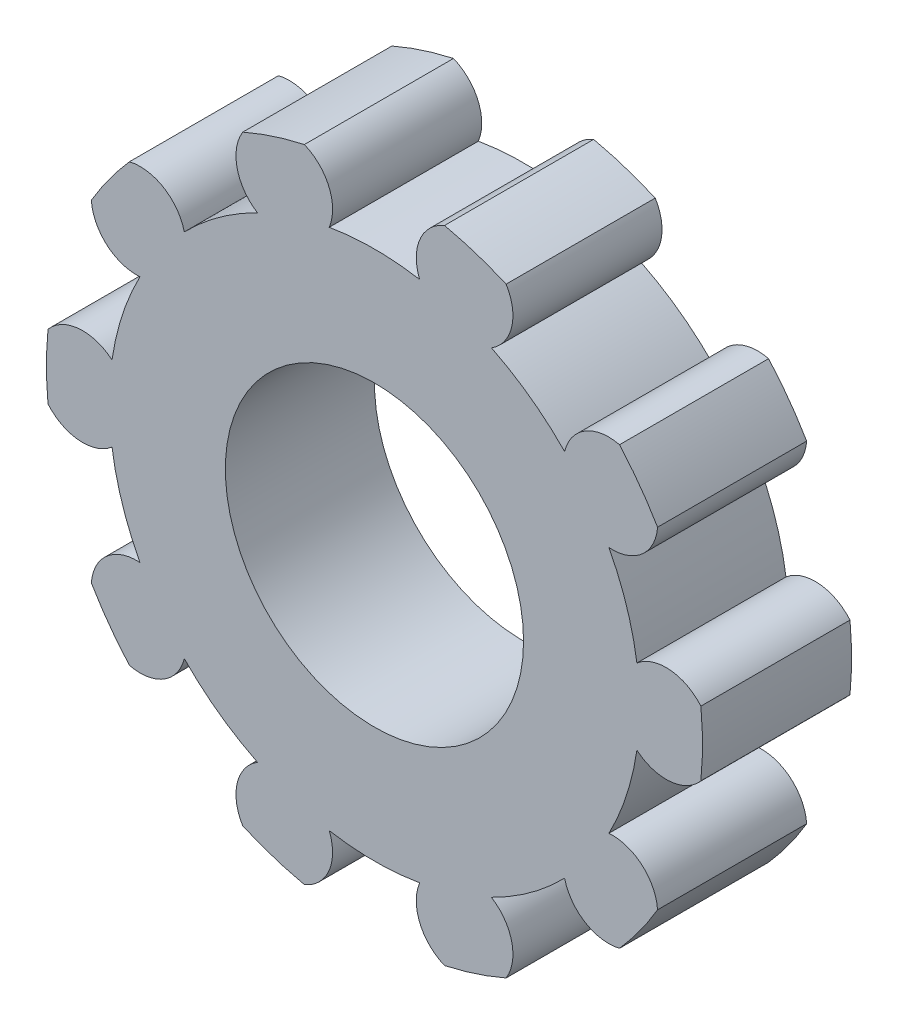
SolidWorks part; units mm, degrees
ref_plane "Front Plane" through (0, 0, 0) normal (0, 0, 1) x (1, 0, 0)
ref_plane "Top Plane" through (0, 0, 0) normal (0, 1, 0) x (1, 0, 0)
ref_plane "Right Plane" through (0, 0, 0) normal (1, 0, 0) x (0, 0, -1)
sketch "Sketch1" plane through (0, 0, 0) normal (0, 0, 1) x (1, 0, 0)
  circle A0 centre (0, 0) radius 6
  circle A1 centre (0, 0) radius 13.2
extrude "Boss-Extrude1" add sketch "Sketch1" along normal blind 6
sketch "Sketch2" plane through (0, 0, 6) normal (0, 0, 1) x (1, 0, 0)
  line L0 (0, 0) -> (0, 15.2) construction
  line L1 (-1.8199, 15.2) -> (0, 0) construction
  line L2 (1.8199, 15.2) -> (0, 0) construction
  arc A0 (-1.8199, 12) -> (1.8199, 12) centre (0, 0) cw
  arc A1 (-2.8199, 12.8953) -> (2.8199, 12.8953) centre (0, 0) cw
  arc A2 (-1.8199, 10.512) -> (1.8199, 10.512) centre (0, 0) cw
  arc A3 (-2.8199, 12.8953) -> (-1.8199, 10.512) centre (-3.5115, 11.2036) cw
  arc A4 (2.8199, 12.8953) -> (1.8199, 10.512) centre (3.5115, 11.2036) ccw
extrude "Cut-Extrude1" cut sketch "Sketch2" against normal through all contours A1 A4 A2 A3
pattern_circular "CirPattern2" count 10 over 360 about axis through (0, 0, 0) along (0, 0, 1) of "Cut-Extrude1"
